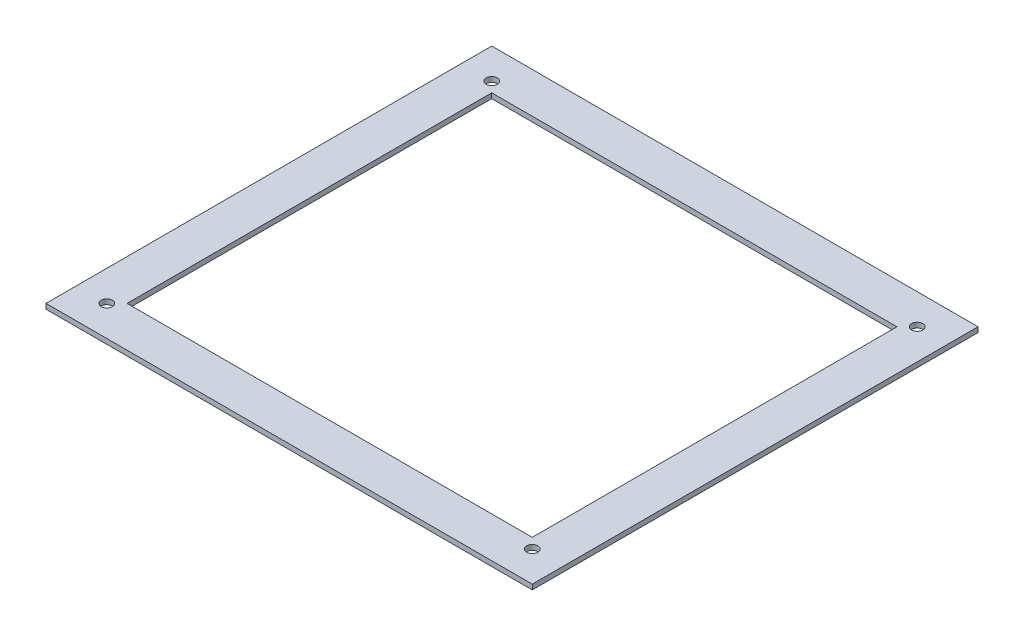
SolidWorks part; units mm, degrees
ref_plane "Front Plane" through (0, 0, 0) normal (0, 0, 1) x (1, 0, 0)
ref_plane "Top Plane" through (0, 0, 0) normal (0, 1, 0) x (1, 0, 0)
ref_plane "Right Plane" through (0, 0, 0) normal (1, 0, 0) x (0, 0, -1)
sketch "Sketch2" plane through (0, 0, 0) normal (0, 1, 0) x (1, 0, 0)
  line L1 (-152.4, -139.7) -> (152.4, -139.7)
  line L2 (-152.4, -139.7) -> (-152.4, 139.7)
  line L3 (-152.4, 139.7) -> (152.4, 139.7)
  line L4 (152.4, -139.7) -> (152.4, 139.7)
  line L5 (-152.4, -139.7) -> (152.4, 139.7) construction
  line L6 (-152.4, 139.7) -> (152.4, -139.7) construction
  line L7 (-127, -114.3) -> (127, -114.3)
  line L8 (-127, -114.3) -> (-127, 114.3)
  line L9 (-127, 114.3) -> (127, 114.3)
  line L10 (127, -114.3) -> (127, 114.3)
  line L11 (-127, -114.3) -> (127, 114.3) construction
  line L12 (-127, 114.3) -> (127, -114.3) construction
  line L13 (-133.35, -120.65) -> (133.35, -120.65)
  line L14 (-133.35, -120.65) -> (-133.35, 120.65)
  line L15 (-133.35, 120.65) -> (133.35, 120.65)
  line L16 (133.35, -120.65) -> (133.35, 120.65)
  line L17 (-133.35, -120.65) -> (133.35, 120.65) construction
  line L18 (-133.35, 120.65) -> (133.35, -120.65) construction
  circle A0 centre (-133.35, 120.65) radius 3.5
  circle A1 centre (133.35, 120.65) radius 3.5
  circle A2 centre (133.35, -120.65) radius 3.5
  circle A3 centre (-133.35, -120.65) radius 3.5
  point P0 (0, 0)
  point P6 (0, 0)
  point P11 (0, 0)
  dimension "D7" = 7
  dimension "D1" = 304.8
  dimension "D2" = 279.4
  dimension "D3" = 25.4
  dimension "D4" = 25.4
  dimension "D5" = 6.35
  dimension "D6" = 6.35
extrude "Boss-Extrude1" add sketch "Sketch2" along normal blind 3.175 contours L1 L4 L3 L2 A3 L14 A0 L15 A1 L16 A2 L13 | A3 L13 A2 L16 A1 L15 A0 L14 L10 L7 L8 L9
